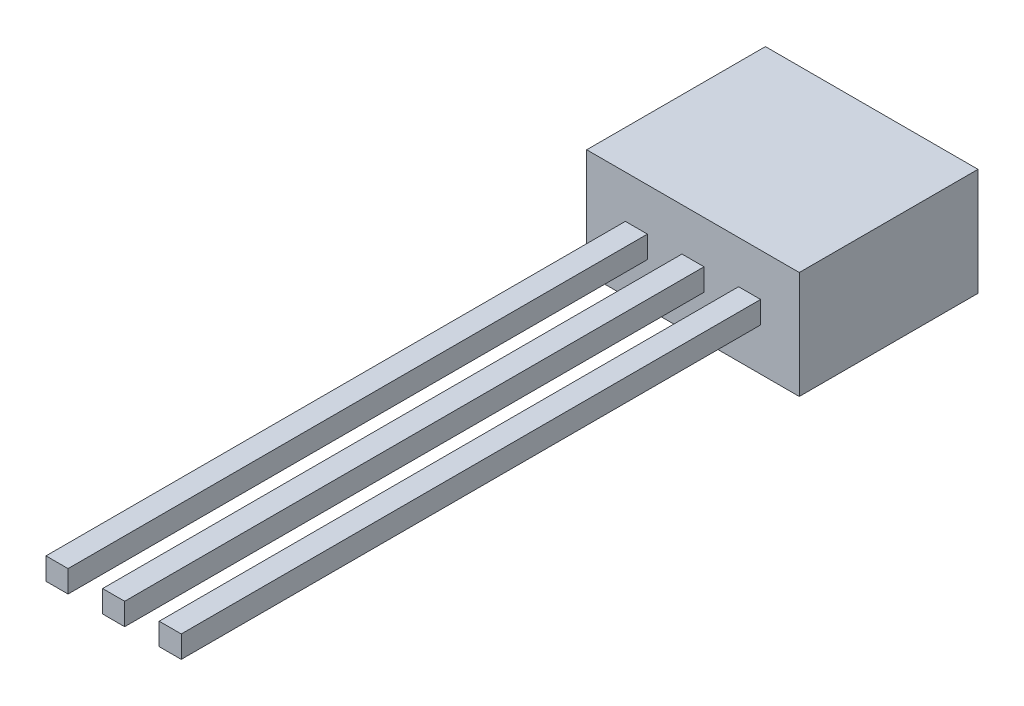
SolidWorks part; units mm, degrees
material "Hexcel AS4C (3000 Filaments)"
ref_plane "Front Plane" through (0, 0, 0) normal (0, 0, 1) x (1, 0, 0)
ref_plane "Top Plane" through (0, 0, 0) normal (0, 1, 0) x (1, 0, 0)
ref_plane "Right Plane" through (0, 0, 0) normal (1, 0, 0) x (0, 0, -1)
sketch "Sketch1" plane through (0, 0, 0) normal (0, 1, 0) x (1, 0, 0)
  line L1 (0, 0) -> (4.77, 0)
  line L2 (0, 0) -> (0, -4.01)
  line L3 (0, -4.01) -> (4.77, -4.01)
  line L4 (4.77, 0) -> (4.77, -4.01)
  dimension "D1" = 4.77
  dimension "D2" = 4.01
extrude "Boss-Extrude1" add sketch "Sketch1" along normal blind 2.41
sketch "Sketch3" plane through (0, 0, 4.01) normal (0, 0, 1) x (1, 0, 0)
  line L0 (0, 2.41) -> (0, 1.205) construction
  line L1 (0, 2.41) -> (0, 0) construction
  line L2 (2.385, 0) -> (2.385, 1.205) construction
  line L3 (0, 0) -> (4.77, 0) construction
  line L4 (0, 1.205) -> (2.385, 1.205) construction
  line L5 (3.4075, 1.4525) -> (3.4075, 0.9575)
  line L6 (2.1375, 1.4525) -> (2.6325, 1.4525)
  line L7 (2.1375, 1.4525) -> (2.1375, 0.9575)
  line L8 (2.1375, 0.9575) -> (2.6325, 0.9575)
  line L9 (2.6325, 1.4525) -> (2.6325, 0.9575)
  line L10 (2.1375, 1.4525) -> (2.6325, 0.9575) construction
  line L11 (2.1375, 0.9575) -> (2.6325, 1.4525) construction
  line L12 (3.4075, 1.4525) -> (3.9025, 1.4525)
  line L13 (3.9025, 1.4525) -> (3.9025, 0.9575)
  line L14 (3.4075, 0.9575) -> (3.9025, 0.9575)
  line L15 (0.8675, 1.4525) -> (0.8675, 0.9575)
  line L16 (0.8675, 1.4525) -> (1.3625, 1.4525)
  line L17 (1.3625, 1.4525) -> (1.3625, 0.9575)
  line L18 (0.8675, 0.9575) -> (1.3625, 0.9575)
  dimension "D1" = 0.495
  dimension "D2" = 0.495
  dimension "D4" = 1.27
  dimension "D6" = 1.27
  dimension "D3" = 2
  dimension "D5" = 2
extrude "Boss-Extrude2" add sketch "Sketch3" along normal blind 13
